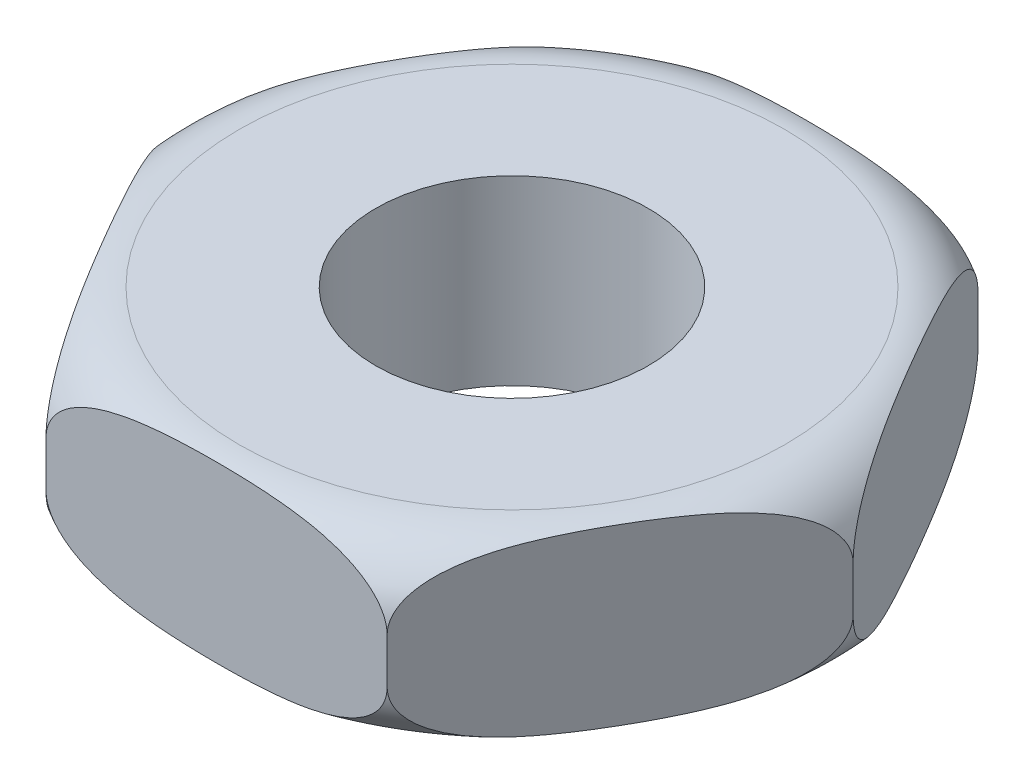
SolidWorks part; units mm, degrees
ref_plane "Front Plane" through (0, 0, 0) normal (0, 0, 1) x (1, 0, 0)
ref_plane "Top Plane" through (0, 0, 0) normal (0, 1, 0) x (1, 0, 0)
ref_plane "Right Plane" through (0, 0, 0) normal (1, 0, 0) x (0, 0, -1)
sketch "Sketch1" plane through (0, 0, 0) normal (0, 1, 0) x (1, 0, 0)
  line L1 (15.0111, 0) -> (7.5056, 13)
  line L2 (7.5056, 13) -> (-7.5056, 13)
  line L3 (-7.5056, 13) -> (-15.0111, 0)
  line L4 (-15.0111, 0) -> (-7.5056, -13)
  line L5 (-7.5056, -13) -> (7.5056, -13)
  line L6 (7.5056, -13) -> (15.0111, 0)
  circle A0 centre (0, 0) radius 13 construction
  circle A1 centre (0, 0) radius 6
  dimension "D2" = 12
  dimension "D1" = 26
extrude "Boss-Extrude1" add sketch "Sketch1" along normal mid plane 8
sketch "Sketch2" plane through (0, 0, 0) normal (0, 0, 1) x (1, 0, 0)
  line L0 (15.0111, 4) -> (15.0111, -4) construction
  line L1 (7.5056, 4) -> (15.0111, 4) construction
  line L2 (15.0111, 4) -> (15.0111, 1)
  line L3 (12.0111, 4) -> (15.0111, 4)
  line L4 (0, 0) -> (0, -50000) construction
  arc A0 (15.0111, 1) -> (12.0111, 4) centre (12.0111, 1) ccw
  dimension "D1" = 6
revolve "Cut-Revolve1" cut sketch "Sketch2" angle 360 about L4
mirror "Mirror1" about plane through (0, 0, 0) normal (0, 1, 0) of "Cut-Revolve1"
